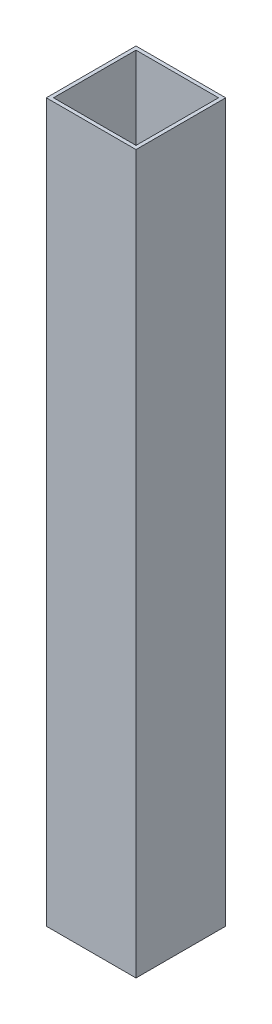
SolidWorks part; units mm, degrees
ref_plane "Спереди" through (0, 0, 0) normal (0, 0, 1) x (1, 0, 0)
ref_plane "Сверху" through (0, 0, 0) normal (0, 1, 0) x (1, 0, 0)
ref_plane "Справа" through (0, 0, 0) normal (1, 0, 0) x (0, 0, -1)
sketch "Эскиз1" plane through (0, 0, 0) normal (0, 1, 0) x (1, 0, 0)
  line L1 (-50, -50) -> (50, -50)
  line L2 (-50, -50) -> (-50, 50)
  line L3 (-50, 50) -> (50, 50)
  line L4 (50, -50) -> (50, 50)
  line L5 (-50, -50) -> (50, 50) construction
  line L6 (-50, 50) -> (50, -50) construction
  point P0 (0, 0)
extrude "Вытянуть-Тонкостенный1" add sketch "Эскиз1" along normal blind 800 thin thin type one direction reverse wall 4
